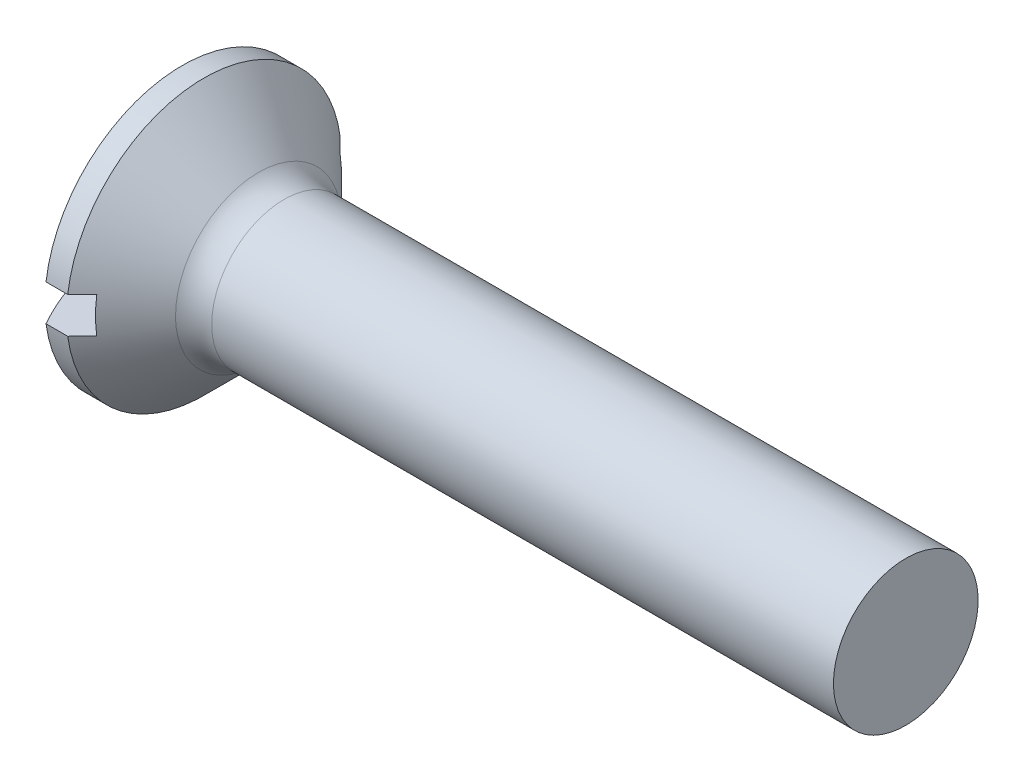
SolidWorks part; units mm, degrees
ref_plane "Plane1" through (0, 0, 0) normal (0, 0, 1) x (1, 0, 0)
ref_plane "Plane2" through (0, 0, 0) normal (0, 1, 0) x (1, 0, 0)
ref_plane "Plane3" through (0, 0, 0) normal (1, 0, 0) x (0, 0, -1)
sketch "BodySke" plane through (0, 0, 0) normal (0, 0, 1) x (1, 0, 0)
  line L0 (0, 0) -> (10.5, 0)
  line L1 (10.5, 0) -> (10.5, 1)
  line L2 (10.5, 1) -> (1.7, 1)
  line L3 (0.8, -1.9) -> (1.7, -1) construction
  line L4 (-15.875, 0) -> (82.55, 0) construction
  line L5 (0.8, 1.9) -> (1.7, 1)
  line L6 (2.1, 4.175) -> (2.1, -11.7) construction
  line L7 (0.5, 2.7793) -> (0.5, -13.0957) construction
  line L8 (0.8, 1.9) -> (0.5, 1.9)
  arc A0 (0, 0) -> (0.5, 1.9) centre (3.86, 0) cw
  dimension "Length" = 10
  dimension "Diameter" = 2
  dimension "Head_dia" = 3.8
  dimension "Head_ang" = 90
  dimension "Advance" = 0.4
  dimension "Thread_nom" = 10
  dimension "Oval_ht" = 0.5
  dimension "Side_ht" = 1.2
revolve "Base-Revolve" add sketch "BodySke"
cosmetic thread "ThreadCosmetic"
extrude "Slot" cut sketch "Sketch2" along normal blind 1
sketch "Sketch2" plane through (0, 0, 0) normal (1, 0, 0) x (0, 0, -1)
  line L0 (1.9, -0.25) -> (-1.9, -0.25)
  line L1 (1.9, -0.25) -> (1.9, 0.25)
  line L2 (-1.9, 0.25) -> (1.9, 0.25)
  line L3 (-1.9, 0.25) -> (-1.9, -0.25)
  dimension "D1" = 3.8
  dimension "Slot_width" = 0.5
  dimension "D3" = 1.9
  dimension "D4" = 0.25
fillet "Fillet1" radius 0.5 1 edges at (1.7, 0, 1)
sketch "ThdSchSke" plane through (0, 0, 0) normal (0, 0, 1) x (1, 0, 0)
  line L0 (2.1, -0.774) -> (1.9418, -1)
  line L1 (2.1, -0.774) -> (2.2582, -1)
  line L2 (2.2582, -1) -> (2.2582, -1.25)
  line L3 (-3.175, 0) -> (5.1513, 0) construction
  line L5 (2.2582, -1.25) -> (1.9418, -1.25)
  line L6 (1.9418, -1.25) -> (1.9418, -1)
  dimension "Thread_minor" = 1.548
  dimension "Diameter" = 2
  dimension "Start" = 2.1
  dimension "SideAngle" = 55
  dimension "VeeAngle" = 70
  dimension "Overcut" = 2.5
revolve "ThreadSchematic" [suppressed] cut sketch "ThdSchSke" angle 360 about L3
pattern_linear "ThdSchPat" [suppressed]
equation "\"D1@Sketch2\" = \"Head_dia@BodySke\""
equation "\"D3@Sketch2\" = \"D1@Sketch2\" / 2"
equation "\"D4@Sketch2\" = \"Slot_width@Sketch2\" / 2"
equation "\"Thread_length@ThreadCosmetic\" = ((sgn( (\"Length@BodySke\" - \"Advance@BodySke\" - \"Side_ht@BodySke\" ) - \"Thread_nom@BodySke\" )-1)*( (\"Length@BodySke\" - \"Advance@BodySke\" - \"Side_ht@BodySke\" ) - \"Thread_nom@BodySke\" ))/-2+ \"Thread_nom@BodySke\""
equation "\"Thread_minor@ThdSchSke\" = \"Thread_minor@ThreadCosmetic\""
equation "\"Diameter@ThdSchSke\" = \"Diameter@BodySke\""
equation "\"Overcut@ThdSchSke\" = \"Diameter@BodySke\" * 1.25"
equation "\"Start@ThdSchSke\" = \"Oval_ht@BodySke\" + \"Length@BodySke\" - \"Thread_length@ThreadCosmetic\"  '---Countersunk---"
equation "\"Num_threads@ThdSchPat\" = int( \"Thread_length@ThreadCosmetic\" / \"Advance@BodySke\" + 0.999 )  + 1"
equation "\"Advance@ThdSchPat\" = \"Thread_length@ThreadCosmetic\" /  (\"Num_threads@ThdSchPat\" - 1) 'relax it"
